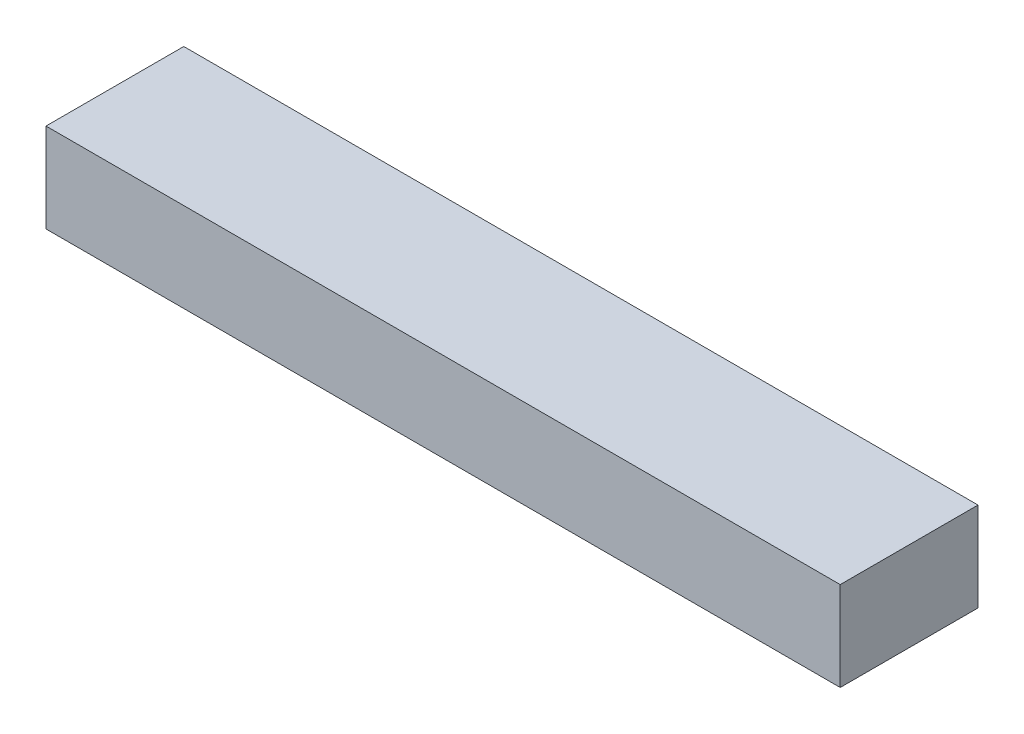
SolidWorks part; units mm, degrees
ref_plane "Front Plane" through (0, 0, 0) normal (0, 0, 1) x (1, 0, 0)
ref_plane "Top Plane" through (0, 0, 0) normal (0, 1, 0) x (1, 0, 0)
ref_plane "Right Plane" through (0, 0, 0) normal (1, 0, 0) x (0, 0, -1)
sketch "Sketch1" plane through (0, 0, 0) normal (0, 1, 0) x (1, 0, 0)
  line L1 (0, 0) -> (-98, 0)
  line L2 (0, 0) -> (0, -17)
  line L3 (0, -17) -> (-98, -17)
  line L4 (-98, 0) -> (-98, -17)
  dimension "D1" = 98
  dimension "D2" = 17
extrude "Boss-Extrude1" add sketch "Sketch1" along normal blind 11
